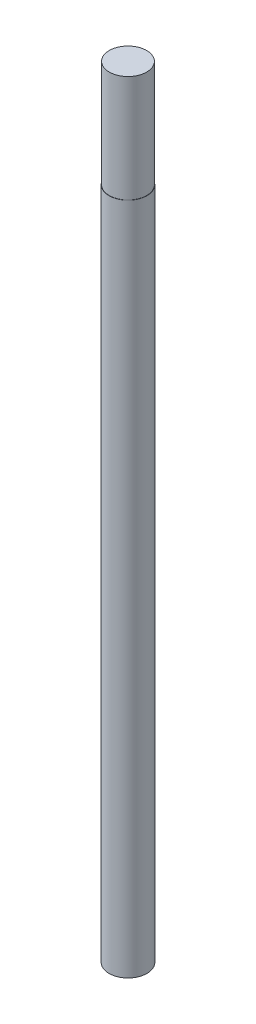
SolidWorks part; units mm, degrees
ref_plane "Front Plane" through (0, 0, 0) normal (0, 0, 1) x (1, 0, 0)
ref_plane "Top Plane" through (0, 0, 0) normal (0, 1, 0) x (1, 0, 0)
ref_plane "Right Plane" through (0, 0, 0) normal (1, 0, 0) x (0, 0, -1)
sketch "Sketch1" plane through (0, 0, 0) normal (0, 1, 0) x (1, 0, 0)
  circle A0 centre (0, 0) radius 3.55
extrude "Extrude1" add sketch "Sketch1" along normal blind 126
sketch "Sketch2" plane through (0, 126, 0) normal (0, 1, 0) x (1, 0, 0)
  circle A0 centre (0, 0) radius 3.5
extrude "Extrude2" add sketch "Sketch2" along normal blind 20
